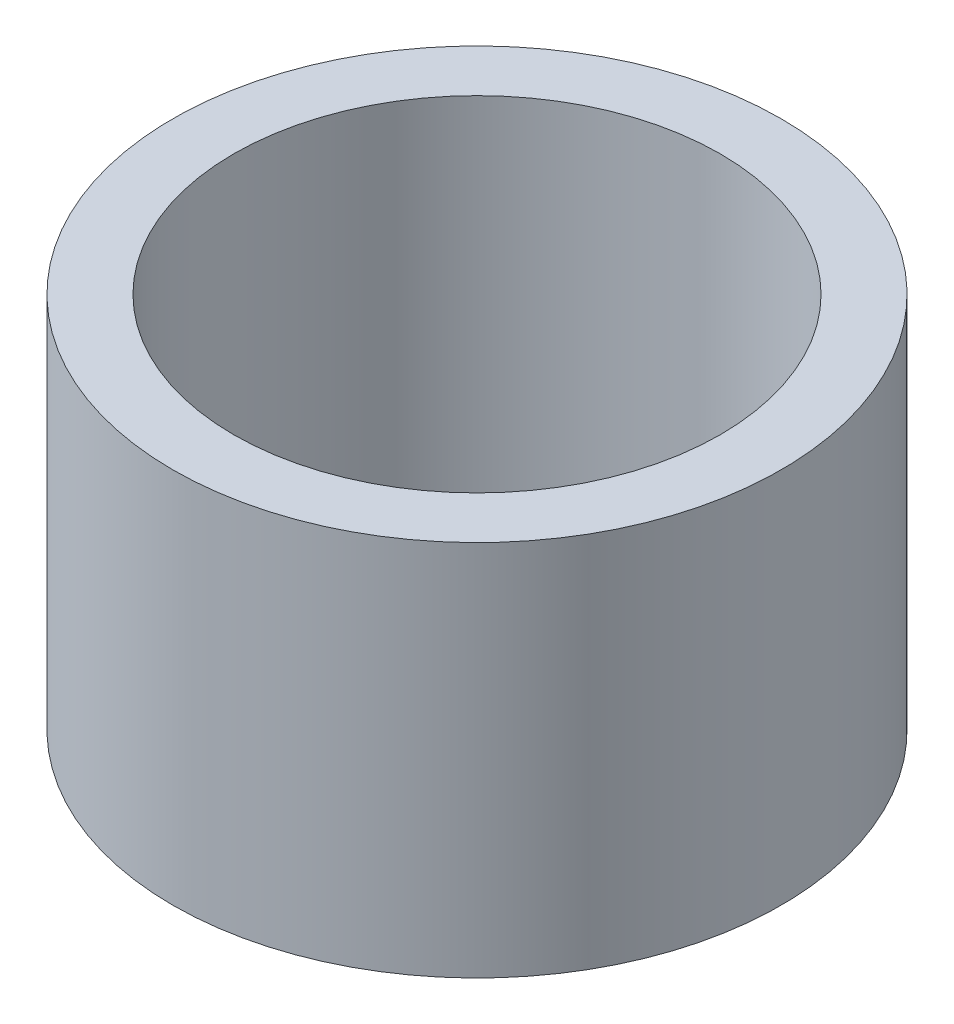
SolidWorks part; units mm, degrees
ref_plane "Front Plane" through (0, 0, 0) normal (0, 0, 1) x (1, 0, 0)
ref_plane "Top Plane" through (0, 0, 0) normal (0, 1, 0) x (1, 0, 0)
ref_plane "Right Plane" through (0, 0, 0) normal (1, 0, 0) x (0, 0, -1)
sketch "Sketch1" plane through (0, 0, 0) normal (0, 1, 0) x (1, 0, 0)
  circle A0 centre (0, 0) radius 6.35
  circle A1 centre (0, 0) radius 7.9375
  dimension "D1" = 12.7
  dimension "D2" = 15.875
extrude "Boss-Extrude1" add sketch "Sketch1" along normal blind 9.8425
